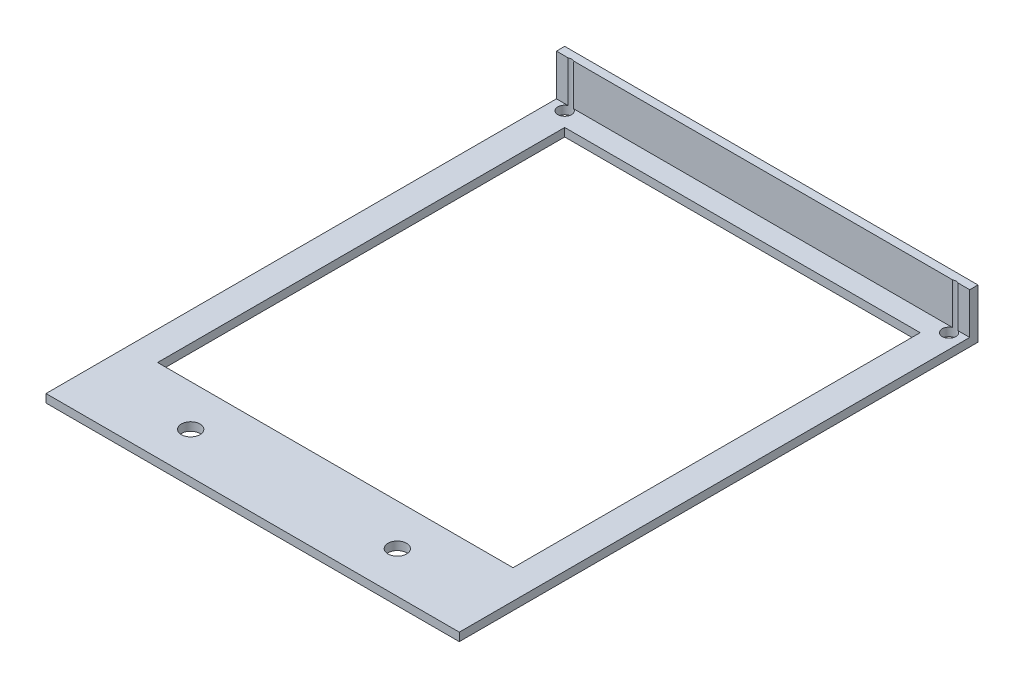
SolidWorks part; units mm, degrees
ref_plane "Front Plane" through (0, 0, 0) normal (0, 0, 1) x (1, 0, 0)
ref_plane "Top Plane" through (0, 0, 0) normal (0, 1, 0) x (1, 0, 0)
ref_plane "Right Plane" through (0, 0, 0) normal (1, 0, 0) x (0, 0, -1)
sketch "Sketch1" plane through (0, 0, 0) normal (0, 1, 0) x (1, 0, 0)
  line L1 (-48, -60.75) -> (48, -60.75)
  line L2 (-48, -60.75) -> (-48, 60.75)
  line L3 (-48, 60.75) -> (48, 60.75)
  line L4 (48, -60.75) -> (48, 60.75)
  line L5 (-48, -60.75) -> (48, 60.75) construction
  line L6 (-48, 60.75) -> (48, -60.75) construction
  line L11 (-43, 55.75) -> (43, 55.75)
  line L12 (-43, 55.75) -> (-43, -42.75)
  line L13 (-43, -42.75) -> (43, -42.75)
  line L14 (43, 55.75) -> (43, -42.75)
  point P0 (0, 0)
  point P6 (0, 0)
  dimension "D1" = 96
  dimension "D2" = 121.5
  dimension "D3" = 18
  dimension "D4" = 5
  dimension "D5" = 5
  dimension "D6" = 5
extrude "Boss-Extrude1" add sketch "Sketch1" along normal blind 2
sketch "Sketch2" plane through (0, 0, 0) normal (0, 1, 0) x (1, 0, 0)
  line L1 (-50, -62.75) -> (50, -62.75)
  line L2 (-50, -62.75) -> (-50, 62.75)
  line L3 (-50, 62.75) -> (50, 62.75)
  line L4 (50, -62.75) -> (50, 62.75)
  line L5 (-50, -62.75) -> (50, 62.75) construction
  line L6 (-50, 62.75) -> (50, -62.75) construction
  line L7 (-48, 60.75) -> (48, 60.75)
  line L8 (-48, 60.75) -> (-48, -60.75)
  line L9 (-48, -60.75) -> (48, -60.75)
  line L10 (48, 60.75) -> (48, -60.75)
  point P0 (0, 0)
  dimension "D1" = 2
  dimension "D2" = 2
extrude "Boss-Extrude2" add sketch "Sketch2" along normal blind 2
sketch "Sketch8" plane through (0, 2, 0) normal (0, 1, 0) x (1, 0, 0)
  line L0 (50, -62.75) -> (50, 62.75) construction
  line L1 (-50, 62.75) -> (50, 62.75)
  line L2 (-50, 62.75) -> (-50, 60.75)
  line L3 (-50, 60.75) -> (50, 60.75)
  line L4 (50, 62.75) -> (50, 60.75)
  dimension "D1" = 2
extrude "Boss-Extrude6" add sketch "Sketch8" along normal blind 10
sketch "Sketch3" plane through (0, 0, 0) normal (0, -1, 0) x (1, 0, 0)
  line L0 (0, 42.75) -> (0, 62.75) construction
  line L1 (-43, 42.75) -> (43, 42.75) construction
  line L2 (-50, 62.75) -> (50, 62.75) construction
  line L3 (0, 52.75) -> (50, 52.75) construction
  line L4 (50, 62.75) -> (50, -62.75) construction
  line L5 (50, -62.75) -> (43, -55.75) construction
  circle A0 centre (25, 52.75) radius 2.25
  circle A1 centre (-25, 52.75) radius 2.25
  circle A2 centre (46.5, -59.25) radius 1.65
  circle A3 centre (-46.5, -59.25) radius 1.65
  dimension "D1" = 4.5
  dimension "D2" = 3.3
extrude "Cut-Extrude1" cut sketch "Sketch3" against normal up to next and the other way through all
